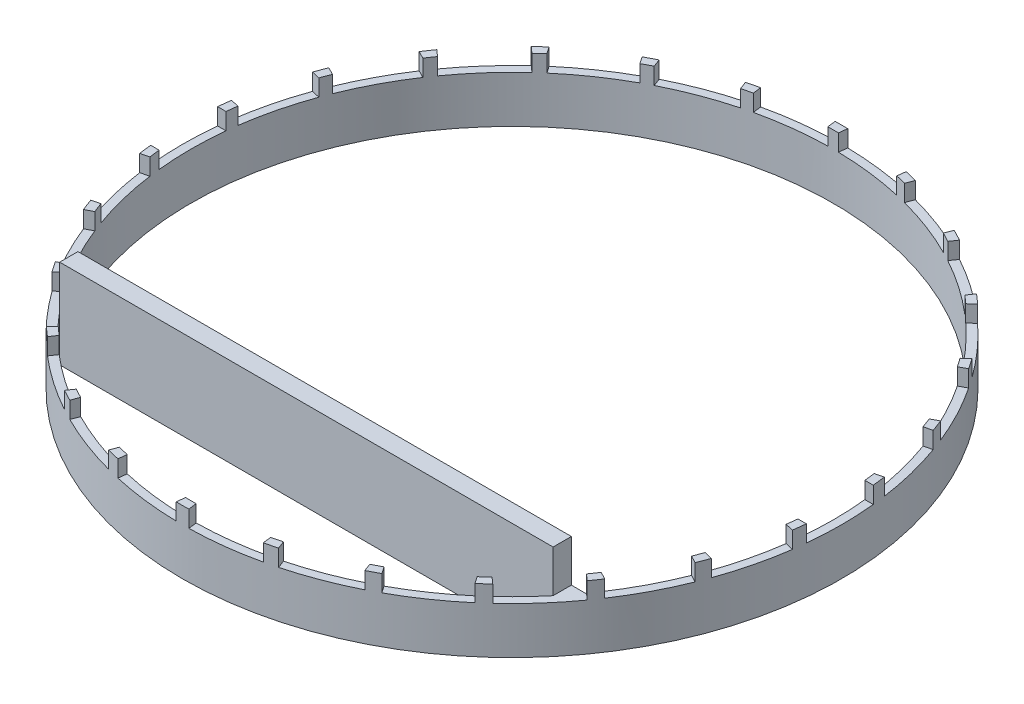
SolidWorks part; units mm, degrees
material "ABS PC"
ref_plane "Front" through (0, 0, 0) normal (0, 0, 1) x (1, 0, 0)
ref_plane "Top" through (0, 0, 0) normal (0, 1, 0) x (1, 0, 0)
ref_plane "Right" through (0, 0, 0) normal (1, 0, 0) x (0, 0, -1)
ref_plane "Plane2" through (0, 0, 56) normal (0, 0, 1) x (1, 0, 0)
sketch "Sketch1" plane through (0, 0, 0) normal (0, 1, 0) x (1, 0, 0)
  line L0 (81.0324, -56) -> (-81.0324, -56) construction
  line L1 (81.0324, -56) -> (77.9744, -56)
  line L2 (-50, -56) -> (50, -56) construction
  line L3 (-77.9744, -56) -> (-81.0324, -56)
  line L4 (76.9735, -61.46) -> (-76.9735, -61.46)
  circle A0 centre (0, 0) radius 96
  circle A1 centre (0, 0) radius 98.5
  dimension "D1" = 197
  dimension "D2" = 192
  dimension "D3" = 5.46
extrude "Boss-Extrude1" add sketch "Sketch1" along normal blind 19 contours L4 A1 L1 A0 | A0 L0 L4 | L3 A1 L4 A0 | L1 A1 L3 A0 | L4 A1 A0
sketch "Sketch2" plane through (0, 0, 0) normal (1, 0, 0) x (0, 0, -1)
  line L0 (-56, 0) -> (96, 0) construction
  line L1 (-10, 25) -> (10, 25)
  line L2 (-10, 25) -> (-10, 14)
  line L3 (-10, 14) -> (10, 14)
  line L4 (10, 25) -> (10, 14)
  line L7 (0, 0) -> (0, 25) construction
  dimension "D2" = 11
  dimension "D3" = 20
  dimension "D4" = 14
extrude "Cut-Extrude1" cut sketch "Sketch2" against normal through all
pattern_circular "CirPattern1" count 26 over 360 about axis through (0, 0, 0) along (0, 1, 0) of "Cut-Extrude1"
sketch "Sketch3" plane through (0, 14, 0) normal (0, 1, 0) x (1, 0, 0)
  line L0 (-77.9744, -56) -> (77.9744, -56) construction
  line L1 (73.7473, -61.46) -> (-73.7473, -61.46)
  line L2 (73.7473, -61.46) -> (73.7473, -56)
  line L3 (73.7473, -56) -> (-73.7473, -56)
  line L4 (-73.7473, -61.46) -> (-73.7473, -56)
extrude "Boss-Extrude2" add sketch "Sketch3" along normal blind 12.6
